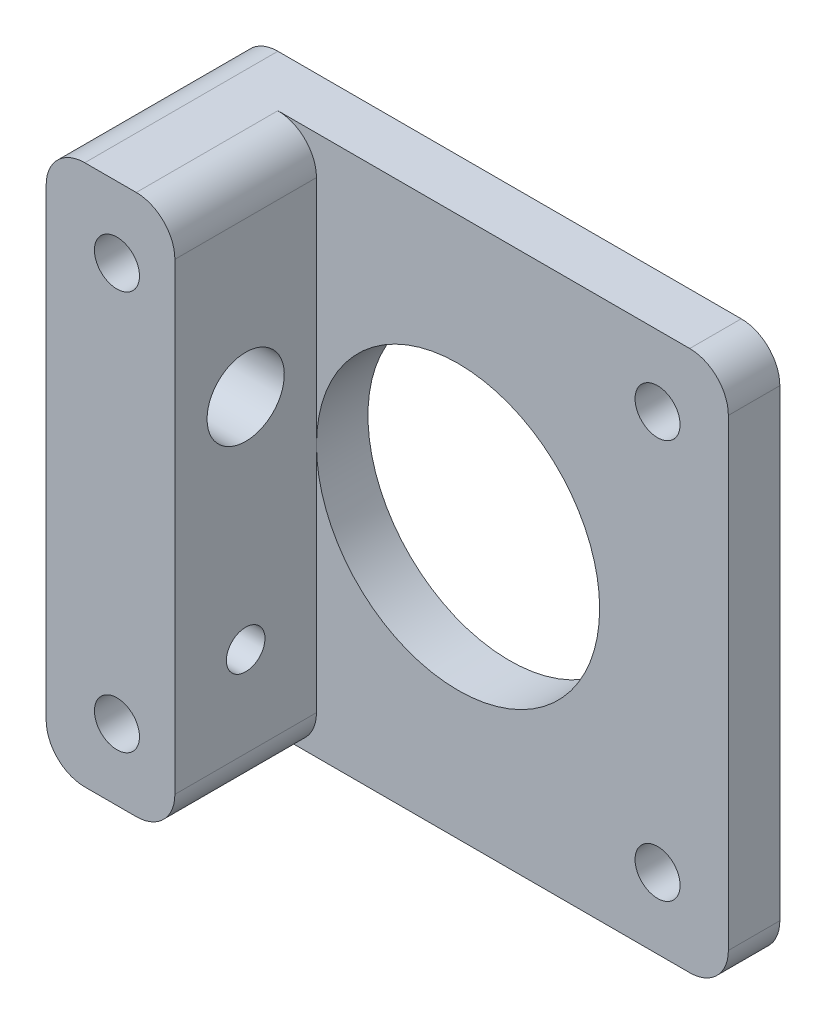
SolidWorks part; units mm, degrees
ref_plane "Front Plane" through (0, 0, 0) normal (0, 0, 1) x (1, 0, 0)
ref_plane "Top Plane" through (0, 0, 0) normal (0, 1, 0) x (1, 0, 0)
ref_plane "Right Plane" through (0, 0, 0) normal (1, 0, 0) x (0, 0, -1)
sketch "Sketch1" plane through (0, 0, 0) normal (0, 0, 1) x (1, 0, 0)
  line L1 (-21, 21) -> (21, 21)
  line L2 (-21, 21) -> (-21, -21)
  line L3 (-21, -21) -> (21, -21)
  line L4 (21, 21) -> (21, -21)
  line L5 (-21, 21) -> (21, -21) construction
  line L6 (-21, -21) -> (21, 21) construction
  point P0 (0, 0)
  dimension "D1" = 42
  dimension "D2" = 42
extrude "Boss-Extrude1" add sketch "Sketch1" along normal blind 4
sketch "Sketch2" plane through (0, 0, 4) normal (0, 0, 1) x (1, 0, 0)
  line L0 (-21, -21) -> (21, -21) construction
  line L1 (-21, 21) -> (-11, 21)
  line L2 (-21, 21) -> (-21, -21)
  line L3 (-21, -21) -> (-11, -21)
  line L4 (-11, 21) -> (-11, -21)
  dimension "D1" = 10
extrude "Boss-Extrude2" add sketch "Sketch2" along normal blind 11
sketch "Sketch3" plane through (0, 0, 4) normal (0, 0, 1) x (1, 0, 0)
  circle A0 centre (0, 0) radius 11
  dimension "D1" = 22
extrude "Cut-Extrude1" cut sketch "Sketch3" against normal blind 11
fillet "Fillet1" radius 3 6 edges at (21, 21, 2) (-21, 21, 7.5) (21, -21, 2) (-21, -21, 7.5) (-11, 21, 9.5) (-11, -21, 9.5)
sketch "Sketch4" plane through (0, 0, 15) normal (0, 0, 1) x (1, 0, 0)
  line L0 (-21, 18) -> (-21, -18) construction
  line L1 (-18, -21) -> (-14, -21) construction
  circle A0 centre (-15.5, 15.5) radius 1.75
  circle A1 centre (-15.5, -15.5) radius 1.75
  circle A2 centre (15.5, 15.5) radius 1.75
  circle A3 centre (15.5, -15.5) radius 1.75
  dimension "D4" = 3.5
  dimension "D5" = 3.5
  dimension "D10" = 3.5
  dimension "D11" = 3.5
  dimension "D1" = 31
  dimension "D2" = 5.5
  dimension "D3" = 5.5
  dimension "D6" = 31
  dimension "D7" = 5.5
  dimension "D8" = 31
  dimension "D9" = 31
extrude "Cut-Extrude2" cut sketch "Sketch4" against normal blind 21
sketch "Sketch6" plane through (-21, 0, 0) normal (-1, 0, 0) x (0, 0, 1)
  line L0 (15, -21) -> (0, -21) construction
  line L1 (0, 21) -> (15, 21) construction
  line L2 (15, 18) -> (15, -18) construction
  circle A0 centre (9.5, 6) radius 3
  circle A1 centre (9.5, -11) radius 1.5
  dimension "D3" = 6
  dimension "D4" = 3
  dimension "D1" = 10
  dimension "D2" = 15
  dimension "D5" = 5.5
  dimension "D6" = 5.5
extrude "Cut-Extrude3" cut sketch "Sketch6" against normal blind 21
